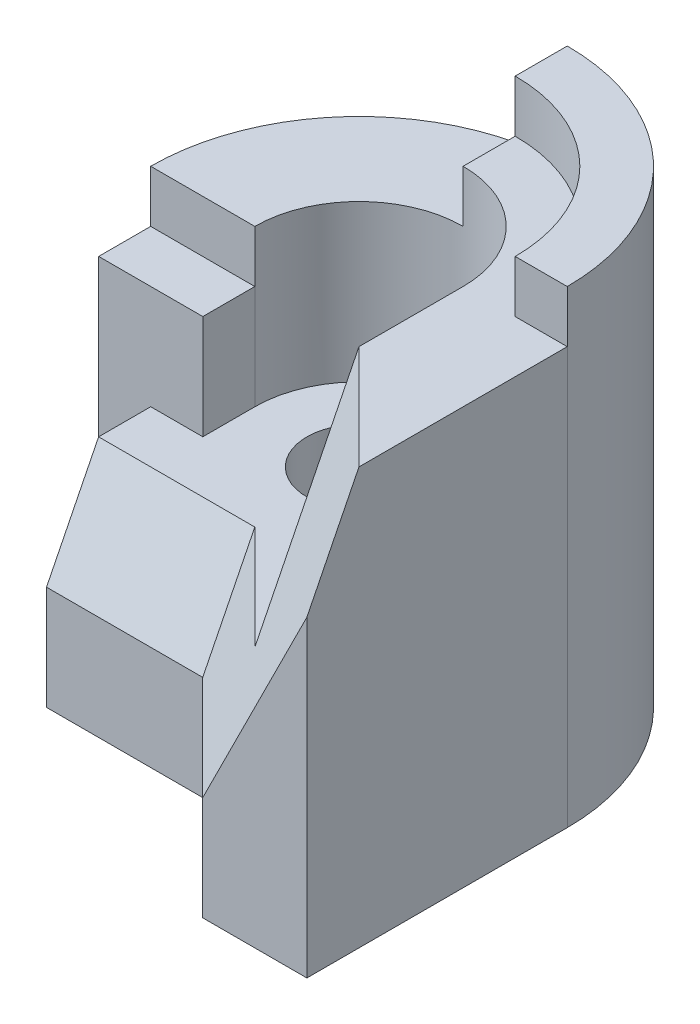
SolidWorks part; units mm, degrees
ref_plane "Front Plane" through (0, 0, 0) normal (0, 0, 1) x (1, 0, 0)
ref_plane "Top Plane" through (0, 0, 0) normal (0, 1, 0) x (1, 0, 0)
ref_plane "Right Plane" through (0, 0, 0) normal (1, 0, 0) x (0, 0, -1)
sketch "Sketch1" plane through (0, 0, 0) normal (0, 1, 0) x (1, 0, 0)
  line L0 (-40, 0) -> (-30, 0)
  line L1 (-30, 0) -> (-30, -30)
  line L2 (-30, -30) -> (0, -30)
  line L3 (0, -30) -> (20, -50)
  line L4 (20, -50) -> (40, -50)
  line L5 (40, -50) -> (40, 0)
  arc A0 (-40, 0) -> (40, 0) centre (0, 0) cw
  dimension "D7" = 40
  dimension "D1" = 50
  dimension "D2" = 20
  dimension "D3" = 20
  dimension "D4" = 30
  dimension "D5" = 10
  dimension "D6" = 20
extrude "Boss-Extrude1" add sketch "Sketch1" along normal blind 90
sketch "Sketch2" plane through (0, 90, 0) normal (0, 1, 0) x (1, 0, 0)
  circle A0 centre (0, 0) radius 10
  dimension "D1" = 20
extrude "Cut-Extrude1" cut sketch "Sketch2" against normal blind 90
sketch "Sketch3" plane through (0, 90, 0) normal (0, 1, 0) x (1, 0, 0)
  line L0 (30, 0) -> (40, 0)
  line L1 (40, -50) -> (40, 0) construction
  line L2 (40, 0) -> (40, -40)
  line L3 (40, -40) -> (20, -20)
  line L4 (20, -20) -> (20, 0)
  line L5 (0, 20) -> (0, 30)
  arc A0 (20, 0) -> (0, 20) centre (0, 0) ccw
  arc A1 (0, 30) -> (30, 0) centre (0, 0) cw
  dimension "D1" = 30
  dimension "D3" = 20
  dimension "D2" = 10
  dimension "D4" = 20
  dimension "D5" = 40
  dimension "D6" = 20
extrude "Cut-Extrude2" cut sketch "Sketch3" against normal blind 10
sketch "Sketch4" plane through (0, 90, 0) normal (0, 1, 0) x (1, 0, 0)
  line L0 (0, 40) -> (0, 20)
  line L1 (-30, 0) -> (-40, 0)
  line L2 (-30, 0) -> (-40, 0)
  line L3 (20, -20) -> (20, -59.2068)
  line L4 (20, -59.2068) -> (-30, -59.2068)
  line L5 (-30, -59.2068) -> (-30, 0)
  line L6 (20, 0) -> (20, -20)
  arc A0 (40, 0) -> (-40, 0) centre (0, 0) ccw construction
  arc A1 (0, 20) -> (20, 0) centre (0, 0) cw
  arc A2 (-40, 0) -> (0, 40) centre (0, 0) cw
extrude "Cut-Extrude3" cut sketch "Sketch4" against normal blind 20
ref_plane "Plane1" through (0, 70, 0) normal (0, 1, 0) x (1, 0, 0)
sketch "Sketch11" plane through (0, 70, 0) normal (0, 1, 0) x (1, 0, 0)
  line L1 (-30, 0) -> (-40, 0)
  line L2 (-30, 0) -> (-30, -9.9861)
  line L3 (-30, -9.9861) -> (-40, -9.9861)
  line L4 (-40, 0) -> (-40, -9.9861)
extrude "Boss-Extrude2" add sketch "Sketch11" against normal blind 70
sketch "Sketch12" plane through (0, 70, 0) normal (0, 1, 0) x (1, 0, 0)
  line L1 (-40, -9.9861) -> (-20, -9.9861)
  line L2 (-40, -9.9861) -> (-40, 0)
  line L3 (-40, 0) -> (-20, 0)
  line L4 (-20, -9.9861) -> (-20, 0)
  dimension "D1" = 20
  dimension "D2" = 9.9861
extrude "Cut-Extrude11" cut sketch "Sketch12" against normal blind 10
sketch "Sketch21" plane through (0, 70, 0) normal (0, 1, 0) x (1, 0, 0)
  line L0 (20, 0) -> (20, -50) construction
  line L1 (-20, 0) -> (-20, -9.9861)
  line L2 (-20, -44.965) -> (20, -44.965)
  line L3 (20, -44.965) -> (20, 0)
  line L4 (-20, -9.9861) -> (-30, -9.9861)
  line L5 (-30, -9.9861) -> (-30, -30)
  line L6 (-30, -30) -> (-20, -30)
  line L7 (-20, -30) -> (-20, -44.965)
  arc A0 (-20, 0) -> (20, 0) centre (0, 0) cw
  arc A1 (20, 0) -> (0, 20) centre (0, 0) ccw construction
extrude "Cut-Extrude25" cut sketch "Sketch21" against normal blind 30
sketch "Sketch22" plane through (-30, 0, 0) normal (-1, 0, 0) x (0, 0, 1)
  line L0 (20, 40) -> (30, 20)
  line L1 (9.9861, 40) -> (30, 40) construction
  line L2 (30, 40) -> (30, 0) construction
  line L3 (30, 20) -> (30, 40)
  line L4 (30, 40) -> (20, 40)
  dimension "D1" = 10
  dimension "D2" = 20
extrude "Cut-Extrude26" cut sketch "Sketch22" against normal blind 30
sketch3d "3DSketch3"
  line L0 (20, 40, 44.965) -> (20, 40, 0) construction
  line L1 (20, 70, 50) -> (20, 0, 50) construction
  line L2 (40, 90, 50) -> (40, 0, 50) construction
  line L3 (0, 20, 30) -> (0, 40, 20)
  line L4 (0, 40, 20) -> (20, 40, 40)
  line L5 (20, 40, 40) -> (20, 80, 20)
  line L6 (20, 80, 20) -> (40, 80, 40)
  line L7 (40, 80, 40) -> (40, 60, 50)
  line L8 (40, 60, 50) -> (20, 20, 50)
  line L9 (20, 20, 50) -> (0, 20, 30)
  point P0 (20, 40, 40)
  point P1 (0, 40, 20)
  point P4 (0, 20, 30)
  point P6 (20, 20, 50)
  point P8 (40, 60, 50)
  point P11 (20, 80, 20)
  point P14 (40, 80, 40)
  dimension "D1" = 20
  dimension "D2" = 30
  dimension "D3" = 40
extrude "Cut-Extrude27" cut sketch "3DSketch3" along direction (0, -1, 0) on the side of the normal blind 83
